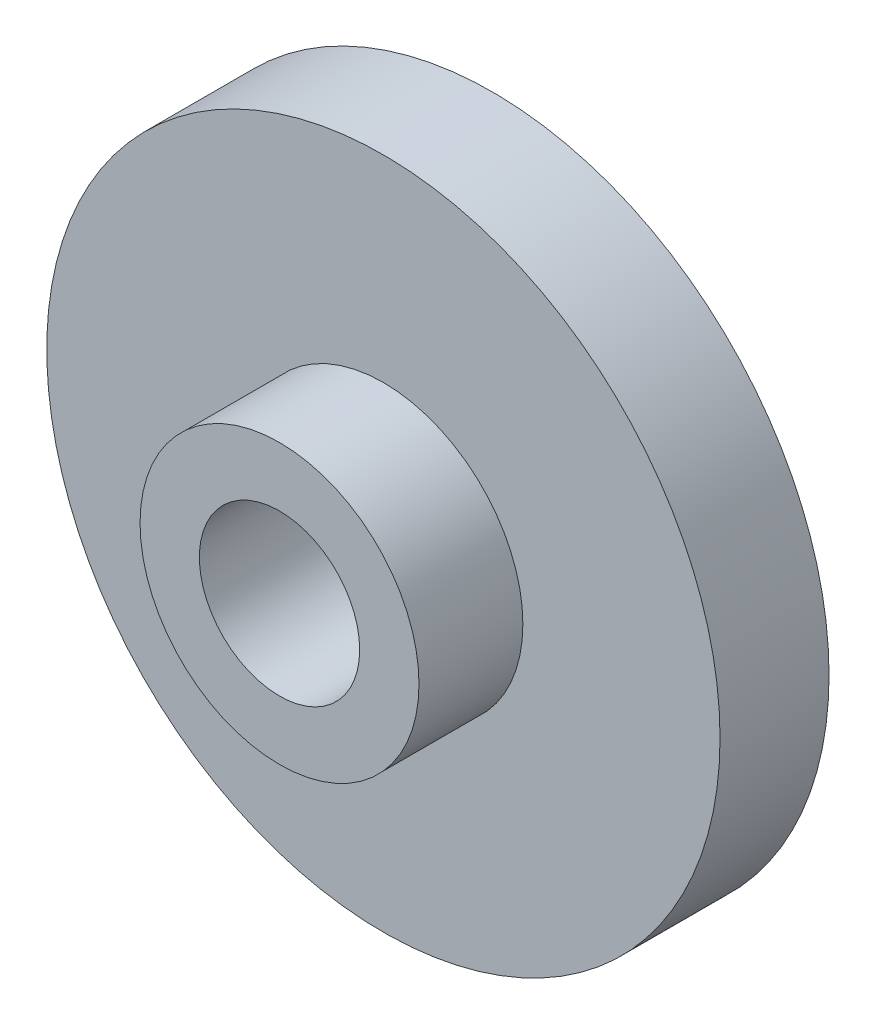
SolidWorks part; units mm, degrees
ref_plane "Alzado" through (0, 0, 0) normal (0, 0, 1) x (1, 0, 0)
ref_plane "Planta" through (0, 0, 0) normal (0, 1, 0) x (1, 0, 0)
ref_plane "Vista lateral" through (0, 0, 0) normal (1, 0, 0) x (0, 0, -1)
sketch "Croquis1" plane through (0, 0, 0) normal (0, 0, 1) x (1, 0, 0)
  circle A0 centre (0, 0) radius 10.5
  dimension "D1" = 21
extrude "Saliente-Extruir1" add sketch "Croquis1" along normal blind 3.4
sketch "Croquis2" plane through (0, 0, 3.4) normal (0, 0, 1) x (1, 0, 0)
  circle A0 centre (0, 0) radius 4.35
  dimension "D1" = 8.7
extrude "Saliente-Extruir2" add sketch "Croquis2" along normal blind 3.24
sketch "Croquis3" plane through (0, 0, 6.64) normal (0, 0, 1) x (1, 0, 0)
  circle A0 centre (0, 0) radius 2.5
  dimension "D1" = 5
extrude "Cortar-Extruir1" cut sketch "Croquis3" against normal blind 16.24
